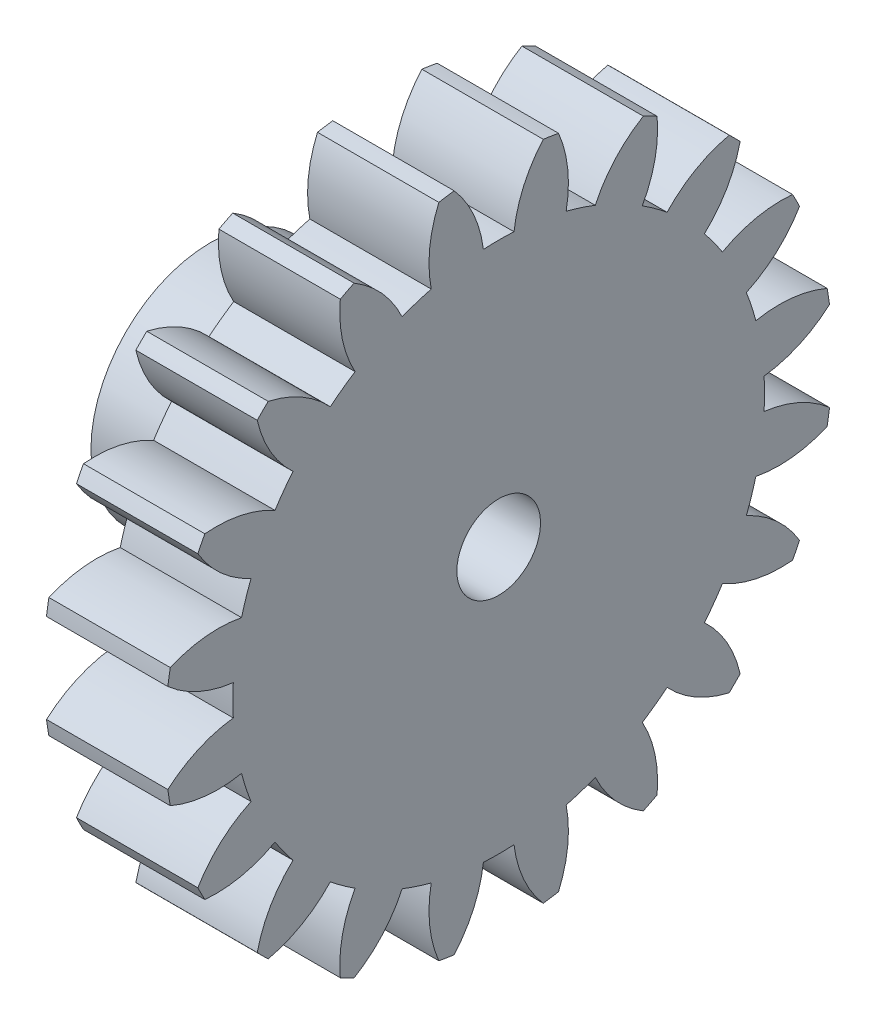
SolidWorks part; units mm, degrees
ref_plane "Plane1" through (0, 0, 0) normal (0, 0, 1) x (1, 0, 0)
ref_plane "Plane2" through (0, 0, 0) normal (0, 1, 0) x (1, 0, 0)
ref_plane "Plane3" through (0, 0, 0) normal (1, 0, 0) x (0, 0, -1)
other "Configuration Table"
sketch "HoldingSke" plane through (0, 0, 0) normal (0, 1, 0) x (1, 0, 0)
  line L0 (0, 0) -> (477.3639, -173.7462)
  line L1 (-15, 0) -> (100, 0) construction
  line L2 (0, 0) -> (-2.1039, 2.3779)
  line L3 (0, 0) -> (-11.863, 4.5341)
  line L4 (0, 0) -> (8.1152, 2.9537)
  line L5 (0, 0) -> (-47.5972, -17.7524)
  line L6 (0, 0) -> (-4.2111, -2.8413)
  line L7 (-2.1039, 2.3779) -> (8.8308, 51.9871)
  line L8 (-76.2, 54.61) -> (-72.771, 54.61)
  line L9 (-71.009, 38.7566) -> (-53.1078, 45.2721)
  line L10 (-76.2, 71.12) -> (104.1128, 71.12)
  line L11 (0, 0) -> (-5.08, 0)
  line L12 (-76.2, 101.6) -> (-76.1492, 101.6)
  line L13 (24.9733, 27.94) -> (52.9518, 28.4284)
  line L14 (24.9733, 27.94) -> (25.0241, 27.9398)
  line L15 (24.9733, 27.94) -> (100.4021, 29.52)
  circle A0 centre (0, 0) radius 1.75
  circle A1 centre (0, 0) radius 11.1252
  circle A2 centre (0, 0) radius 38.1
  circle A3 centre (0, 0) radius 1.75
  dimension "MHD" = 22.2504
  dimension "Hub_dia" = 76.2
  dimension "Bore" = 3.5
  dimension "MBD" = 3.5
  dimension "Num_teeth" = 20
  dimension "Pitch" = 508
  dimension "Overall_len" = 50.8
  dimension "Show_teeth" = 20
  dimension "Thickness" = 5.08
  dimension "OAL" = 50.8001
  dimension "T_dim" = 3.429
  dimension "Ap" = 20
  dimension "H" = 19.05
  dimension "Pitch_radius" = 180.3128
  dimension "Width" = 5.08
  dimension "Backlash" = 0.0508
  dimension "Addendum_fac" = 1
  dimension "Dedendum_fac" = 1.2
  dimension "Clearance_fac" = 0.2
  dimension "Dedendum_add" = 0.0508
sketch "BasProSke" plane through (0, 0, 0) normal (0, 1, 0) x (1, 0, 0)
  line L0 (-10, 0) -> (60, 0) construction
  line L1 (0, 0) -> (0, 13.97)
  line L2 (0, 0) -> (5.08, 0)
  line L3 (5.08, 0) -> (5.08, 13.97)
  line L4 (5.08, 13.97) -> (0, 13.97)
  dimension "Thickness" = 5.08
  dimension "Diameter" = 27.94
revolve "Base-Revolve" add sketch "BasProSke" angle 360 about L0
sketch "TooCutSke" plane through (0, 0, 0) normal (1, 0, 0) x (0, 0, -1)
  line L1 (0, 0) -> (0, 107) construction
  line L2 (0, 0) -> (-1.0853, 12.6535) construction
  line L3 (0, 0) -> (-3.9633, 25.0231) construction
  line L4 (-1.0853, 12.6535) -> (-1.9816, 12.5116) construction
  arc A0 (0.6405, 11.1067) -> (-0.6405, 11.1067) centre (0, 0) ccw
  arc A1 (1.8856, 13.8678) -> (-1.8856, 13.8678) centre (0, 0) ccw
  circle A2 centre (0, 0) radius 12.7 construction
  circle A3 centre (0, 0) radius 11.9341 construction
  arc A4 (-0.6405, 11.1067) -> (-1.8856, 13.8678) centre (-5.6834, 10.4939) ccw
  arc A5 (1.8856, 13.8678) -> (0.6405, 11.1067) centre (5.6834, 10.4939) ccw
  dimension "Root_dia" = 22.2504
  dimension "Overcut_dia" = 27.9908
  dimension "Pitch_dia" = 25.4
  dimension "Base_dia" = 23.8682
  dimension "Flank_rad" = 5.08
  dimension "Half_ang" = 9
  dimension "Half_CT" = 0.9075
extrude "ToothCut" cut sketch "TooCutSke" along normal through all
fillet "Breaks" [suppressed] radius 0.0254
fillet "RootFillets" [suppressed] radius 0.3048
pattern_circular "TeethCuts" count 20 every 18 about axis through (-10, 0, 0) along (1, 0, 0) of "ToothCut", "RootFillets", "Breaks"
sketch "HubNeaOneSke" plane through (0, 0, 0) normal (-1, 0, 0) x (0, 0, 1)
  circle A0 centre (0, 0) radius 11.1252
  dimension "Diameter" = 22.2504
extrude "HubNearOne" [suppressed] add sketch "HubNeaOneSke" along normal blind 45.7201
sketch "HubNeaBotSke" plane through (0, 0, 0) normal (-1, 0, 0) x (0, 0, 1)
  circle A0 centre (0, 0) radius 11.1252
  dimension "Diameter" = 22.2504
extrude "HubNearBoth" [suppressed] add sketch "HubNeaBotSke" along normal blind 22.86
ref_plane "FarPln" through (5.08, 0, 0) normal (1, 0, 0) x (0, 0, -1)
sketch "HubFarSke" plane through (5.08, 0, 0) normal (1, 0, 0) x (0, 0, -1)
  circle A0 centre (0, 0) radius 11.1252
  dimension "Diameter" = 22.2504
extrude "HubFar" [suppressed] add sketch "HubFarSke" along normal blind 22.86
sketch "BorSke" plane through (0, 0, 0) normal (1, 0, 0) x (0, 0, -1)
  circle A0 centre (0, 0) radius 1.75
  dimension "Diameter" = 3.5
extrude "Bore" cut sketch "BorSke" along normal mid plane 101.6001
sketch "KeySke" plane through (0, 0, 0) normal (1, 0, 0) x (0, 0, -1)
  line L0 (-0.127, 0) -> (-0.127, 1.679)
  line L1 (-0.127, 1.679) -> (0.127, 1.679)
  line L2 (0.127, 1.679) -> (0.127, 0)
  line L3 (0, 0) -> (0, 34) construction
  line L4 (-0.127, 0) -> (0.127, 0)
  dimension "Offset" = 1.679
  dimension "Width" = 0.254
extrude "Keyway" [suppressed] cut sketch "KeySke" along normal mid plane 101.6001
pattern_circular "Keyway2" [suppressed] count 2 every 90 about axis through (-10, 0, 0) along (1, 0, 0)
sketch "Sketch1" plane through (0, 0, 0) normal (-1, 0, 0) x (0, 0, 1)
  circle A0 centre (0, 0) radius 5
  circle A1 centre (0, 0) radius 1.75
  dimension "D1" = 10
extrude "Boss-Extrude1" add sketch "Sketch1" along normal blind 6.985
sketch "Sketch3" plane through (-6.985, 0, 0) normal (-1, 0, 0) x (0, 0, 1)
  circle A0 centre (0, 0) radius 3
  dimension "D1" = 6
extrude "Cut-Extrude1" cut sketch "Sketch3" against normal blind 3.81
sketch "Sketch4" plane through (-6.985, 0, 0) normal (-1, 0, 0) x (0, 0, 1)
  line L0 (-0.25, 3.127) -> (0.25, 3.127)
  line L1 (-0.4843, 3) -> (0.5773, 3) construction
  line L2 (0, 3) -> (0, 3.127) construction
  line L3 (-0.25, 3.127) -> (0, 2.694)
  line L4 (0, 2.694) -> (0.25, 3.127)
  circle A0 centre (0, 0) radius 3 construction
  dimension "D1" = 0.127
  dimension "D2" = 0.5
  dimension "D3" = 60
extrude "Boss-Extrude2" add sketch "Sketch4" against normal up to surface (3.81 mm away) up to face at (-3.175, 0, 1.75)
pattern_circular "CirPattern1" count 36 over 360 about axis through (0, 0, 0) along (1, 0, 0) of "Boss-Extrude2"
equation "' \"Pitch@HoldingSke\" = 4"
equation "' \"Num_teeth@HoldingSke\" = 12"
equation "' \"Ap@HoldingSke\" =  20"
equation "' \"Ap@HoldingSke\" = 20"
equation "' \"Width@HoldingSke\" = 0.5"
equation "' \"Hub_dia@HoldingSke\"= 1"
equation "' \"Hub_dia@HoldingSke\" = 1"
equation "' \"Overall_len@HoldingSke\" = 1.0"
equation "' \"Bore@HoldingSke\" = 0.75"
equation "' \"T_dim@HoldingSke\" = 0.85"
equation "' \"Width@KeySke\" = 0.25"
equation "' \"Show_teeth@HoldingSke\" = 13"
equation "' \"Backlash@HoldingSke\" = 0.009"
equation "' \"Addendum_fac@HoldingSke\" = 1.0"
equation "' \"Dedendum_fac@HoldingSke\" = 1.25"
equation "' \"Dedendum_add@HoldingSke\" = 0.00005"
equation "' \"Clearance_fac@HoldingSke\" = 0.25"
equation "' \"Pitch@HoldingSke\" = 0.5"
equation "' \"Num_teeth@HoldingSke\" = 23"
equation "' \"Show_teeth@HoldingSke\" = 23"
equation "' \"Backlash@HoldingSke\" = 0.0375"
equation "\"Overcut_dia@TooCutSke\" = (\"Num_teeth@HoldingSke\" + 2 * \"Addendum_fac@HoldingSke\") / \"Pitch@HoldingSke\" + 0.002"
equation "\"Pitch_dia@TooCutSke\" = \"Num_teeth@HoldingSke\" / \"Pitch@HoldingSke\""
equation "\"Base_dia@TooCutSke\" = \"Num_teeth@HoldingSke\" / \"Pitch@HoldingSke\" * cos((\"Ap@HoldingSke\"  * 3.14159265 / 180))"
equation "\"Root_dia@TooCutSke\" = (\"Num_teeth@HoldingSke\" + 2) / \"Pitch@HoldingSke\" - 2 * (\"Addendum_fac@HoldingSke\" + \"Dedendum_fac@HoldingSke\") / \"Pitch@HoldingSke\" - \"Dedendum_add@HoldingSke\" * 2"
equation "\"Half_ang@TooCutSke\" = 180 / \"Num_teeth@HoldingSke\""
equation "\"Half_CT@TooCutSke\" = \"Num_teeth@HoldingSke\" / \"Pitch@HoldingSke\" * sin((3.14159265 / 2 / \"Num_teeth@HoldingSke\")) / 2 - 7 * \"Backlash@HoldingSke\" / 4"
equation "\"Flank_rad@TooCutSke\" = \"Num_teeth@HoldingSke\" / \"Pitch@HoldingSke\" / 5"
equation "\"Radius@RootFillets\" = \"Clearance_fac@HoldingSke\" / \"Pitch@HoldingSke\" + \"Dedendum_add@HoldingSke\""
equation "\"Break_rad@Breaks\" = 0.02 / \"Pitch@HoldingSke\""
equation "\"Thickness@HoldingSke\" = \"Width@HoldingSke\""
equation "\"OAL@HoldingSke\" = \"Thickness@HoldingSke\""
equation "\"MHD@HoldingSke\" = (\"Num_teeth@HoldingSke\" + 2) / \"Pitch@HoldingSke\" - 2 * (\"Addendum_fac@HoldingSke\" + \"Dedendum_fac@HoldingSke\")  / \"Pitch@HoldingSke\" - \"Dedendum_add@HoldingSke\" * 2"
equation "\"MBD@HoldingSke\" = (\"Num_teeth@HoldingSke\" + 2) / \"Pitch@HoldingSke\" - 2 * (\"Addendum_fac@HoldingSke\" + \"Dedendum_fac@HoldingSke\")  / \"Pitch@HoldingSke\" - \"Dedendum_add@HoldingSke\" * 2 - 0.002"
equation "\"MHD@HoldingSke\" = ((sgn( \"MHD@HoldingSke\" - \"Hub_dia@HoldingSke\" )-1)*( \"MHD@HoldingSke\" - \"Hub_dia@HoldingSke\" ))/-2+ \"Hub_dia@HoldingSke\""
equation "\"MBD@HoldingSke\" = ((sgn( \"MBD@HoldingSke\" - \"Bore@HoldingSke\" )-1)*( \"MBD@HoldingSke\" - \"Bore@HoldingSke\" ))/-2+ \"Bore@HoldingSke\""
equation "\"OAL@HoldingSke\" = ((sgn( \"OAL@HoldingSke\" - \"Overall_len@HoldingSke\" )+1)*( \"OAL@HoldingSke\" - \"Overall_len@HoldingSke\" ))/2 + \"Overall_len@HoldingSke\" + 0.000002"
equation "\"Num_teeth@TeethCuts\" = int( \"Show_teeth@HoldingSke\" ) + 1"
equation "\"Num_teeth@TeethCuts\" = ((sgn( \"Num_teeth@TeethCuts\" - \"Num_teeth@HoldingSke\" )-1)*( \"Num_teeth@TeethCuts\" - \"Num_teeth@HoldingSke\" ))/-2+ \"Num_teeth@HoldingSke\""
equation "\"Num_teeth@TeethCuts\" = ((sgn( \"Num_teeth@TeethCuts\" - 2.0)+1)*( \"Num_teeth@TeethCuts\" - 2.0))/2 +2.0"
equation "\"Angle@TeethCuts\" = 360.0 / \"Num_teeth@HoldingSke\""
equation "\"Diameter@BasProSke\" = (\"Num_teeth@HoldingSke\" + 2 * \"Addendum_fac@HoldingSke\") / \"Pitch@HoldingSke\""
equation "\"Thickness@BasProSke\"  = \"Thickness@HoldingSke\""
equation "' \"Fillet_rad@BasProSke\" =  \"Thickness@HoldingSke\" * 0.05"
equation "' \"Fillet_rad@BasProSke\" = \"Thickness@HoldingSke\" * 0.05"
equation "\"MHD@HoldingSke\" = ((sgn( \"MHD@HoldingSke\" - \"Root_dia@TooCutSke\" )-1)*( \"MHD@HoldingSke\" - \"Root_dia@TooCutSke\" ))/-2+ \"Root_dia@TooCutSke\""
equation "\"Diameter@HubNeaOneSke\" = \"MHD@HoldingSke\""
equation "\"Length@HubNearOne\" = \"OAL@HoldingSke\" - \"Thickness@BasProSke\""
equation "\"Diameter@HubNeaBotSke\" = \"MHD@HoldingSke\""
equation "\"Length@HubNearBoth\" = ( \"OAL@HoldingSke\" - \"Thickness@BasProSke\" ) / 2.0"
equation "\"Thickness@FarPln\" = \"Thickness@BasProSke\""
equation "\"Diameter@HubFarSke\" = \"MHD@HoldingSke\""
equation "\"Length@HubFar\" = ( \"OAL@HoldingSke\" - \"Thickness@BasProSke\" ) / 2.0"
equation "\"Diameter@BorSke\" = \"MBD@HoldingSke\""
equation "\"D1@Bore\" = \"OAL@HoldingSke\" * 2.0"
equation "\"D1@Keyway\" = \"OAL@HoldingSke\" * 2.0"
equation "\"Offset@KeySke\" = \"T_dim@HoldingSke\" - \"MBD@HoldingSke\" / 2.0"
